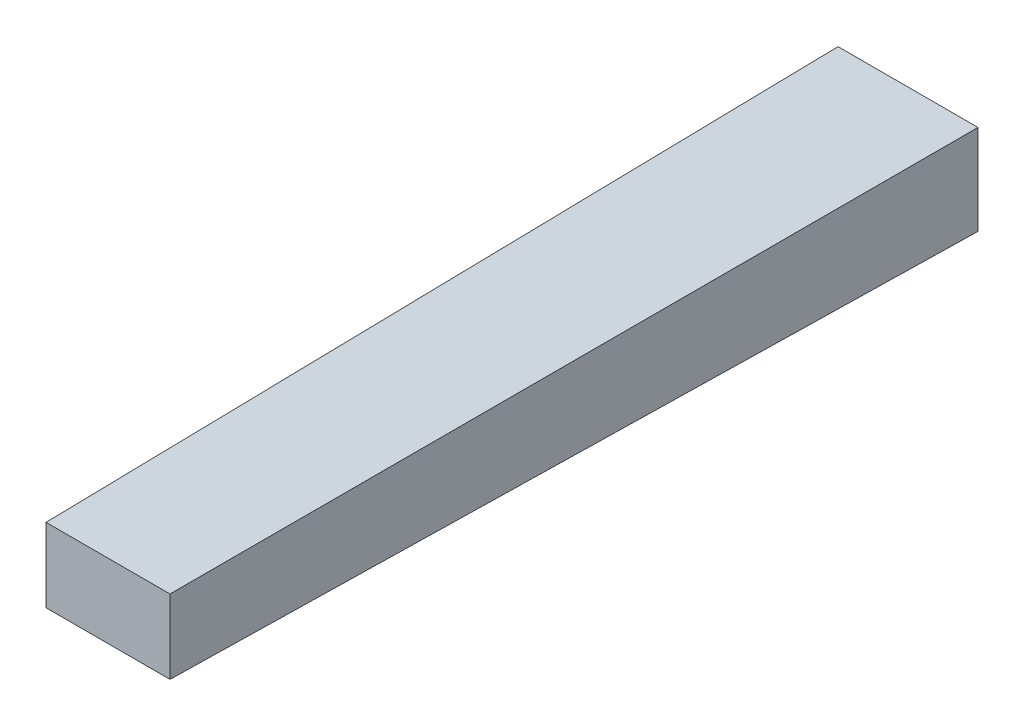
SolidWorks part; units mm, degrees
ref_plane "Front Plane" through (0, 0, 0) normal (0, 0, 1) x (1, 0, 0)
ref_plane "Top Plane" through (0, 0, 0) normal (0, 1, 0) x (1, 0, 0)
ref_plane "Right Plane" through (0, 0, 0) normal (1, 0, 0) x (0, 0, -1)
sketch "Sketch2" plane through (0, 0, 0) normal (0, 0, 1) x (1, 0, 0)
  line L1 (0, 0) -> (14, 0)
  line L2 (0, 0) -> (0, 9)
  line L3 (0, 9) -> (14, 9)
  line L4 (14, 0) -> (14, 9)
  dimension "D1" = 14
  dimension "D2" = 9
extrude "Boss-Extrude1" add sketch "Sketch2" along normal blind 80 draft 0.573
